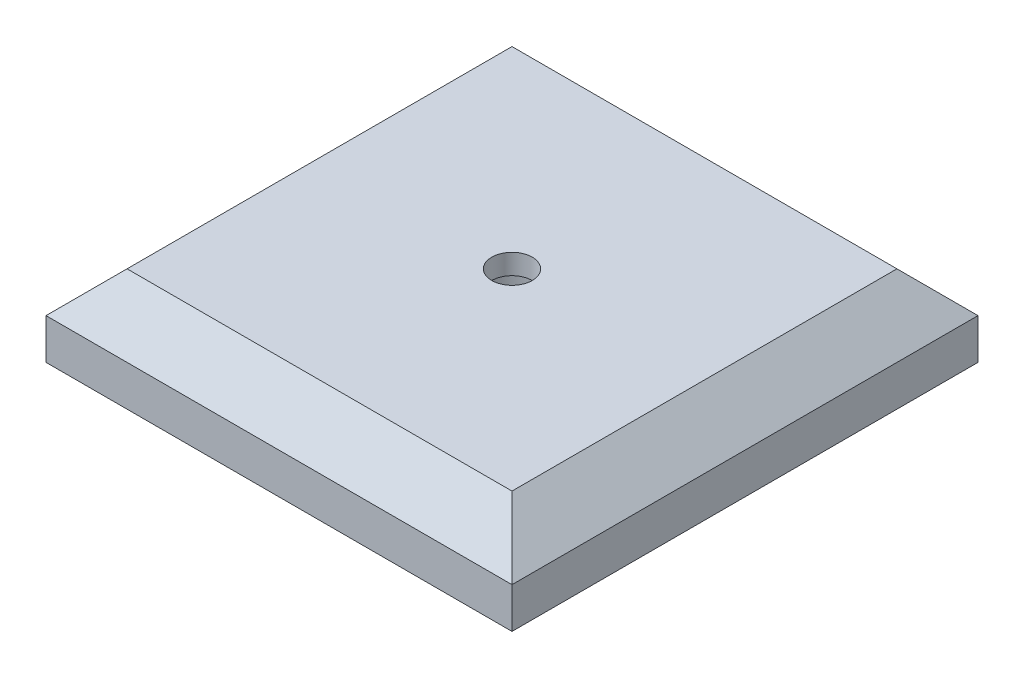
SolidWorks part; units mm, degrees
ref_plane "Front Plane" through (0, 0, 0) normal (0, 0, 1) x (1, 0, 0)
ref_plane "Top Plane" through (0, 0, 0) normal (0, 1, 0) x (1, 0, 0)
ref_plane "Right Plane" through (0, 0, 0) normal (1, 0, 0) x (0, 0, -1)
sketch "Sketch2" plane through (0, 0, 0) normal (0, 1, 0) x (1, 0, 0)
  line L1 (-36.5125, -36.5125) -> (36.5125, -36.5125)
  line L2 (-36.5125, -36.5125) -> (-36.5125, 36.5125)
  line L3 (-36.5125, 36.5125) -> (36.5125, 36.5125)
  line L4 (36.5125, -36.5125) -> (36.5125, 36.5125)
  point P0 (0, 0)
  dimension "D1" = 73.025
  dimension "D2" = 73.025
extrude "Boss-Extrude1" add sketch "Sketch2" along normal blind 12.7
sketch "Sketch3" plane through (0, 12.7, 0) normal (0, 1, 0) x (1, 0, 0)
  circle A0 centre (0, 0) radius 3.175
  dimension "D1" = 6.35
extrude "Cut-Extrude1" cut sketch "Sketch3" against normal blind 3.175
sketch "Sketch4" plane through (0, 0, 0) normal (0, -1, 0) x (1, 0, 0)
  circle A0 centre (0, 0) radius 6.35
  dimension "D1" = 12.7
extrude "Cut-Extrude2" cut sketch "Sketch4" against normal blind 9.525
chamfer "Chamfer2" distance 6.35 angle 45 4 edges at (-36.5125, 12.7, 0) (0, 12.7, -36.5125) (36.5125, 12.7, 0) (0, 12.7, 36.5125)
